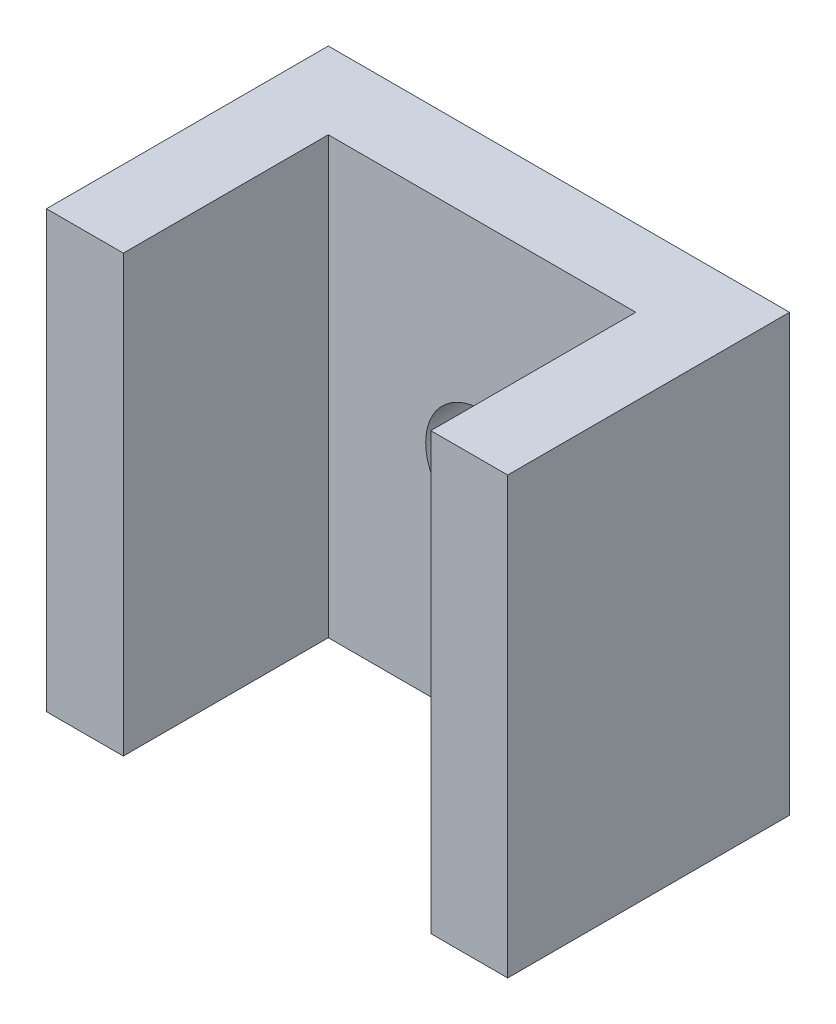
SolidWorks part; units mm, degrees
ref_plane "Front Plane" through (0, 0, 0) normal (0, 0, 1) x (1, 0, 0)
ref_plane "Top Plane" through (0, 0, 0) normal (0, 1, 0) x (1, 0, 0)
ref_plane "Right Plane" through (0, 0, 0) normal (1, 0, 0) x (0, 0, -1)
sketch "Sketch1" plane through (0, 0, 0) normal (0, 1, 0) x (1, 0, 0)
  line L0 (0, 0) -> (0, 11)
  line L1 (0, 11) -> (18, 11)
  line L2 (18, 11) -> (18, 0)
  line L3 (18, 0) -> (15, 0)
  line L4 (15, 0) -> (15, 8)
  line L5 (15, 8) -> (3, 8)
  line L6 (3, 8) -> (3, 0)
  line L7 (3, 0) -> (0, 0)
  dimension "D1" = 3
  dimension "D2" = 3
  dimension "D3" = 12
  dimension "D4" = 8
  dimension "D5" = 3
extrude "Boss-Extrude1" add sketch "Sketch1" along normal blind 17
sketch "Sketch2" plane through (0, 0, -11) normal (0, 0, -1) x (-1, 0, 0)
  line L0 (-18, 17) -> (-18, 0) construction
  line L1 (-18, 17) -> (0, 17) construction
  circle A0 centre (-9, 8.5) radius 2.2
  dimension "D1" = 9
  dimension "D2" = 8.5
extrude "Cut-Extrude1" cut sketch "Sketch2" against normal blind 17
